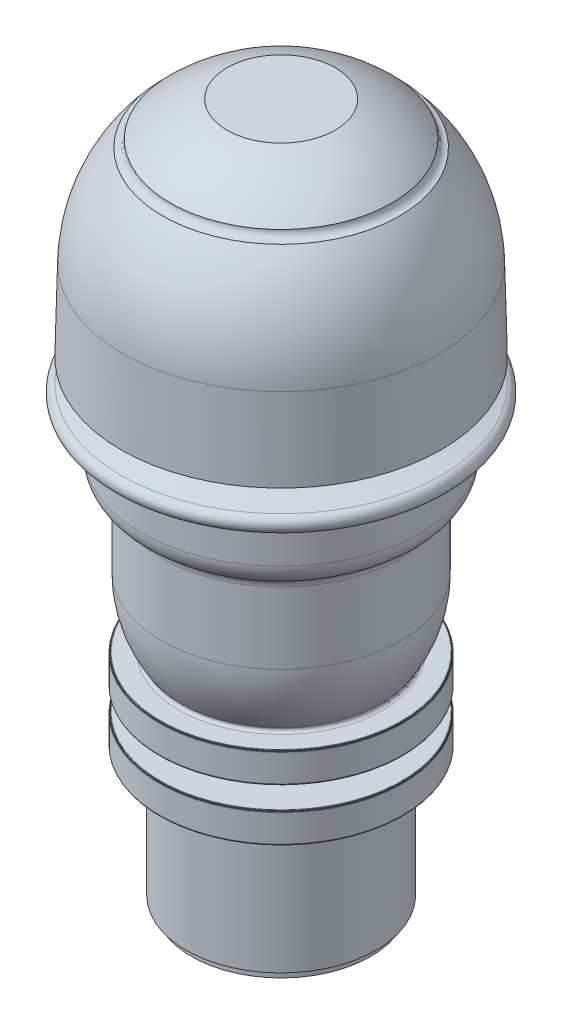
SolidWorks part; units mm, degrees
ref_plane "Alzado" through (0, 0, 0) normal (0, 0, 1) x (1, 0, 0)
ref_plane "Planta" through (0, 0, 0) normal (0, 1, 0) x (1, 0, 0)
ref_plane "Vista lateral" through (0, 0, 0) normal (1, 0, 0) x (0, 0, -1)
sketch "Croquis1" plane through (0, 0, 0) normal (0, 0, 1) x (1, 0, 0)
  line L0 (0, 127.2) -> (-0.5649, 127.2)
  line L1 (-3.7118, 127.2) -> (-0.5649, 127.2)
  line L2 (-9.1679, 127.2) -> (-3.7118, 127.2)
  line L3 (-18.4679, 84.8) -> (-19.8179, 84.8)
  line L4 (-29.1686, 86.4) -> (-28.8098, 101.3708)
  line L5 (-9.8595, 127.2) -> (-9.1679, 127.2)
  line L6 (0, 79.4511) -> (-28.3797, 79.4511)
  line L7 (-22.6237, 77) -> (-22.6665, 79.4511)
  line L8 (-29.1561, 82.3489) -> (-20.0084, 84.8)
  line L9 (-20.0084, 84.8) -> (0, 84.8)
  line L10 (0, 0) -> (-11.402, 0)
  line L11 (-22.9679, 77) -> (-22.6237, 77)
  line L12 (-16.3179, 1.5) -> (-17.3179, 1.5)
  line L13 (-17.3179, 1.5) -> (-17.3179, 24.9145)
  line L14 (-17.3179, 24.9145) -> (-21.9014, 24.9945)
  line L15 (-21.9014, 24.9945) -> (-21.9568, 25.0006)
  line L16 (-21.9568, 25.0006) -> (-22.0292, 25.0255)
  line L17 (-22.0292, 25.0255) -> (-22.1228, 25.0979)
  line L18 (-22.1228, 25.0979) -> (-22.1772, 25.1897)
  line L19 (-22.1772, 25.1897) -> (-22.1961, 25.2944)
  line L20 (-22.1961, 25.2944) -> (-22.1961, 30.2056)
  line L21 (-22.1961, 30.2056) -> (-22.1735, 30.3198)
  line L22 (-22.1735, 30.3198) -> (-22.1086, 30.4173)
  line L23 (-22.1086, 30.4173) -> (-22.0153, 30.4809)
  line L24 (-22.0153, 30.4809) -> (-21.9523, 30.5003)
  line L25 (-21.9523, 30.5003) -> (-21.9014, 30.5055)
  line L26 (-21.9014, 30.5055) -> (-14.3626, 30.6371)
  line L27 (-14.0679, 30.9371) -> (-14.0679, 34.0629)
  line L28 (-14.3626, 34.3629) -> (-21.9014, 34.4945)
  line L29 (-21.9014, 34.4945) -> (-21.9568, 34.5006)
  line L30 (-21.9568, 34.5006) -> (-22.0292, 34.5255)
  line L31 (-22.0292, 34.5255) -> (-22.1228, 34.5979)
  line L32 (-22.1228, 34.5979) -> (-22.1772, 34.6897)
  line L33 (-22.1772, 34.6897) -> (-22.1961, 34.7944)
  line L34 (-22.1961, 34.7944) -> (-22.1961, 39.7056)
  line L35 (-22.1961, 39.7056) -> (-22.1735, 39.8198)
  line L36 (-22.1735, 39.8198) -> (-22.1086, 39.9173)
  line L37 (-22.1086, 39.9173) -> (-22.0153, 39.9809)
  line L38 (-22.0153, 39.9809) -> (-21.9523, 40.0003)
  line L39 (-21.9523, 40.0003) -> (-21.9014, 40.0055)
  line L40 (-21.9014, 40.0055) -> (-18.6235, 40.0627)
  line L41 (-21.8179, 52.6) -> (-21.8179, 65.6)
  line L42 (-25.4679, 71.4419) -> (-25.4679, 77)
  line L43 (-25.4679, 77) -> (0, 77)
  line L44 (-11.402, 0) -> (-16.3179, 0)
  line L45 (-16.3179, 0) -> (-16.3179, 1.5)
  line L46 (-29.1686, 86.4) -> (0, 86.4)
  line L51 (-16.3179, 1.5) -> (0, 1.5)
  line L93 (-18.6235, 40.0627) -> (0, 40.0627)
  line L94 (-21.9014, 34.4945) -> (0, 34.4945)
  line L95 (-21.9906, 25.0123) -> (0, 25.0123)
  line L96 (-21.947, 30.5008) -> (0, 30.5008)
  line L97 (0, 0) -> (0, 127.2) construction
  arc A0 (-21.567, 119.5009) -> (-28.8098, 101.3708) centre (-0.8179, 100.7) ccw
  arc A1 (-21.567, 119.5009) -> (-20.2179, 120.8901) centre (-21.6179, 120.9) ccw
  arc A2 (-9.8595, 127.2) -> (-20.2179, 120.8901) centre (-0.8179, 100.7) ccw
  arc A3 (-29.1561, 82.3489) -> (-28.3797, 79.4511) centre (-28.7679, 80.9) ccw
  arc A4 (-17.3929, 84.8) -> (-16.5929, 86.4) centre (-17.3929, 85.8) ccw
  arc A5 (-14.3626, 30.6371) -> (-14.0679, 30.9371) centre (-14.3679, 30.9371) ccw
  arc A6 (-14.0679, 34.0629) -> (-14.3626, 34.3629) centre (-14.3679, 34.0629) ccw
  arc A7 (-18.6235, 40.0627) -> (-18.218, 40.8426) centre (-18.6323, 40.5627) ccw
  arc A8 (-21.8179, 52.6) -> (-18.218, 40.8426) centre (-0.8179, 52.6) ccw
  arc A9 (-21.8179, 65.6) -> (-22.941, 67.3975) centre (-23.8179, 65.6) ccw
  arc A10 (-25.4679, 71.4419) -> (-22.941, 67.3975) centre (-20.9679, 71.4419) ccw
revolve "Revolución1" add sketch "Croquis1" angle 360 about L97
